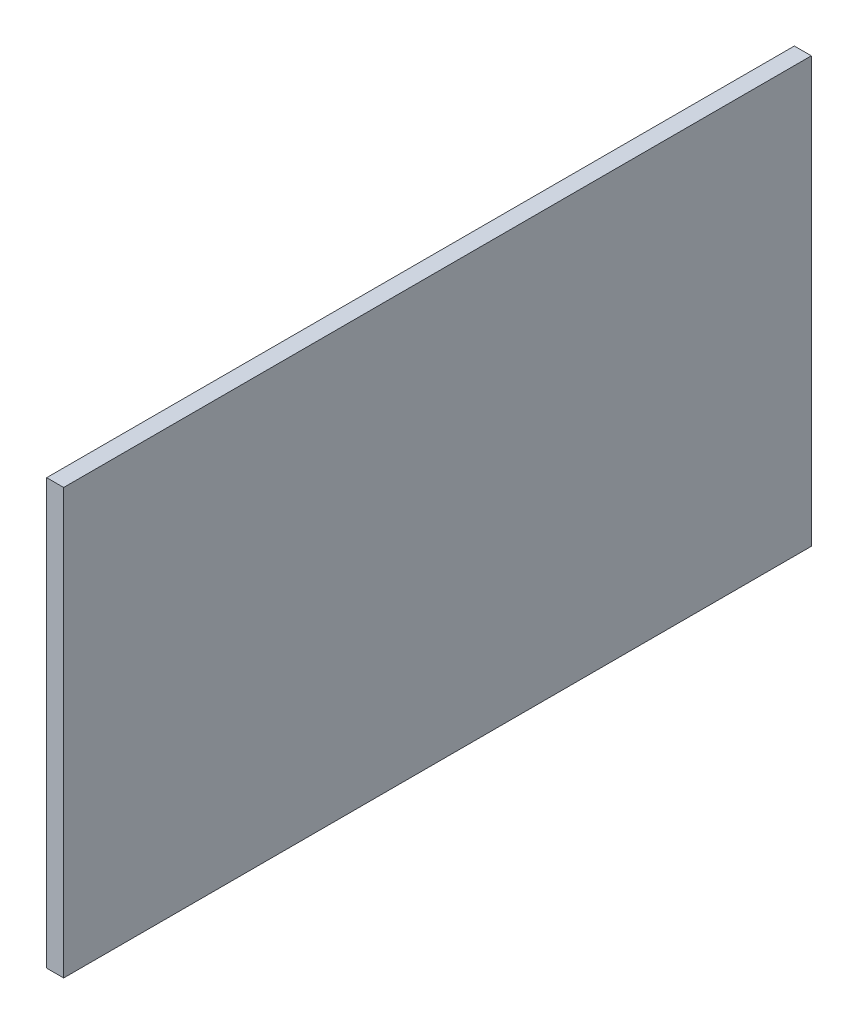
SolidWorks part; units mm, degrees
ref_plane "Front Plane" through (0, 0, 0) normal (0, 0, 1) x (1, 0, 0)
ref_plane "Top Plane" through (0, 0, 0) normal (0, 1, 0) x (1, 0, 0)
ref_plane "Right Plane" through (0, 0, 0) normal (1, 0, 0) x (0, 0, -1)
sketch "Sketch2" plane through (0, 0, 0) normal (1, 0, 0) x (0, 0, -1)
  line L1 (0, 0) -> (220, 0)
  line L2 (0, 0) -> (0, 125)
  line L3 (0, 125) -> (220, 125)
  line L4 (220, 0) -> (220, 125)
  dimension "D1" = 220
  dimension "D2" = 125
extrude "Boss-Extrude1" add sketch "Sketch2" against normal blind 5
sketch "Sketch3" plane through (0, 0, 0) normal (1, 0, 0) x (0, 0, -1)
  line L0 (220, 125) -> (0, 125) construction
  line L1 (0, 0) -> (220, 0) construction
  line L2 (0, 125) -> (0, 0) construction
  circle A0 centre (12.5, 100) radius 1.25
  circle A1 centre (12.5, 25) radius 1.25
  dimension "D1" = 2.5
  dimension "D2" = 2.5
  dimension "D3" = 25
  dimension "D4" = 25
  dimension "D5" = 12.5
  dimension "D6" = 12.5
extrude "Cut-Extrude1" [suppressed] cut sketch "Sketch3" against normal through all
sketch "Sketch14" plane through (0, 0, 0) normal (1, 0, 0) x (0, 0, -1)
  line L0 (0, 70) -> (220, 70) construction
  line L1 (0, 125) -> (0, 0) construction
  line L2 (220, 0) -> (220, 125) construction
  line L3 (220, 125) -> (0, 125) construction
  dimension "D1" = 55
sketch "Sketch15" plane through (0, 0, 0) normal (1, 0, 0) x (0, 0, -1)
  text T0 "FOOD\r\nCONTAINMENT UNIT" font "Futura XBlk BT" height in points 48
ref_plane "Plane6" through (0, 0, -110) normal (0, 0, 1) x (1, 0, 0)
mirror "Mirror2" [suppressed] about plane through (0, 0, -110) normal (0, 0, 1)
extrude "Cut-Extrude2" [suppressed] cut sketch "Sketch15" against normal blind 1
